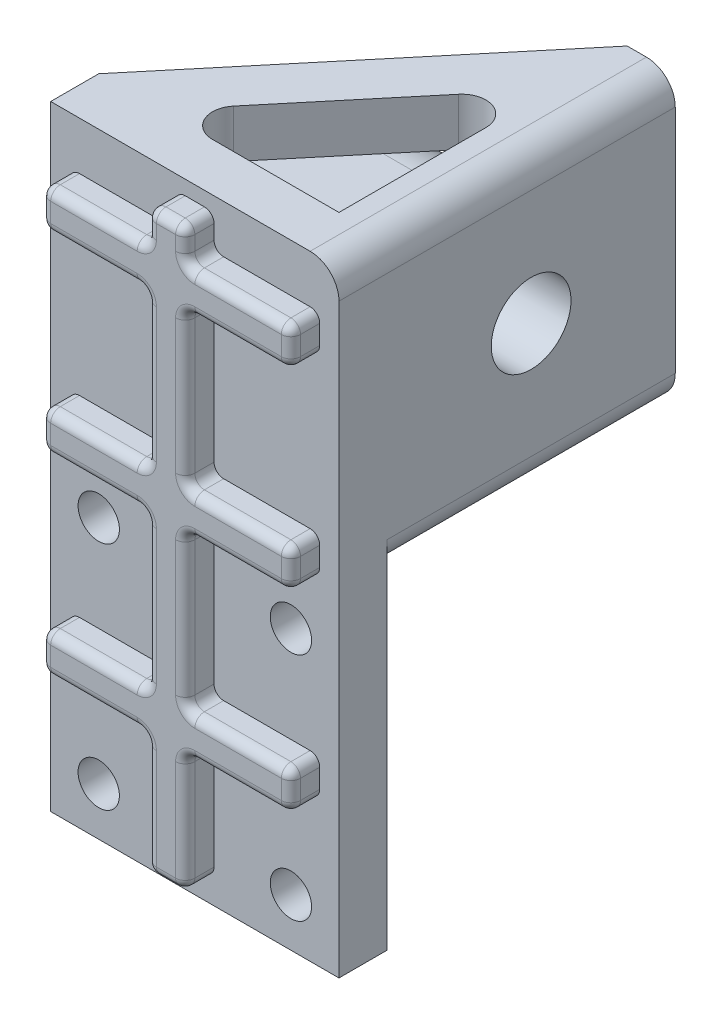
SolidWorks part; units mm, degrees
material "Balsa"
ref_plane "前视基准面" through (0, 0, 0) normal (0, 0, 1) x (1, 0, 0)
ref_plane "上视基准面" through (0, 0, 0) normal (0, 1, 0) x (1, 0, 0)
ref_plane "右视基准面" through (0, 0, 0) normal (1, 0, 0) x (0, 0, -1)
other "Configuration Table"
sketch "Sketch3" plane through (0, 0, 0) normal (0, 0, 1) x (1, 0, 0)
  line L0 (15, 0) -> (15, -34) construction
  line L1 (0, 0) -> (30, 0)
  line L2 (0, 0) -> (0, -34)
  line L3 (0, -34) -> (30, -34)
  line L4 (30, 0) -> (30, -34)
  line L5 (0, -17) -> (30, -17) construction
  circle A0 centre (5, -5) radius 2.15
  circle A1 centre (25, -5) radius 2.15
  circle A2 centre (5, -29) radius 2.15
  circle A3 centre (25, -29) radius 2.15
  point P6 (15, 0)
  dimension "D3" = 4.3
  dimension "D4" = 20
  dimension "D5" = 24
  dimension "D1" = 34
  dimension "D2" = 30
extrude "Boss-Extrude1" add sketch "Sketch3" along normal blind 5
sketch "Sketch5" plane through (0, 0, 0) normal (0, 0, -1) x (-1, 0, 0)
  line L1 (-30, 0) -> (0, 0)
  line L2 (-30, 0) -> (-30, 30)
  line L3 (-30, 30) -> (0, 30)
  line L4 (0, 0) -> (0, 30)
  line L5 (-30, 30) -> (-25, 30)
  line L6 (-30, 30) -> (-30, 0)
  line L7 (-30, 0) -> (-25, 0)
  line L8 (-25, 30) -> (-25, 0)
  dimension "D1" = 30
  dimension "D2" = 5
  dimension "D3" = 30
extrude "Boss-Extrude4" add sketch "Sketch5" against normal up to surface (5 mm away) contours L2 L1 L4 L3 | L6 L5 L8 L7 up to face at (2.85, -29, 5)
sketch "Sketch6" plane through (0, 0, 0) normal (0, 0, -1) x (-1, 0, 0)
  line L0 (-30, 0) -> (-30, 30) construction
  line L1 (-30, 0) -> (0, 0) construction
  line L2 (0, 0) -> (0, 30) construction
  line L3 (-30, 30) -> (0, 30) construction
  line L4 (-30, 30) -> (-25, 30) construction
  line L5 (-25, 30) -> (-25, 0) construction
  line L6 (-30, 0) -> (-25, 0) construction
  line L7 (-30, 30) -> (-30, 0) construction
  line L8 (-30, 0) -> (-30, 30)
  line L9 (-30, 0) -> (0, 0)
  line L10 (0, 0) -> (0, 30)
  line L11 (-30, 30) -> (0, 30)
  line L12 (-30, 30) -> (-25, 30)
  line L13 (-25, 30) -> (-25, 0)
  line L14 (-30, 0) -> (-25, 0)
  line L15 (-30, 30) -> (-30, 0)
  line M3 (-30, 30) -> (-30, -34)
extrude "Boss-Extrude5" add sketch "Sketch6" along normal blind 30 contours L13 L11 L9 M3
sketch "Sketch7" plane through (0, 0, 5) normal (0, 0, 1) x (1, 0, 0)
  line L0 (15, 30) -> (15, -34) construction
  line L1 (30, 30) -> (0, 30) construction
  line L2 (0, -34) -> (30, -34) construction
  line L3 (2, 5) -> (2, 1)
  line L4 (13, 28.5) -> (17, 28.5)
  line L5 (13, 28.5) -> (13, -31.5)
  line L6 (13, -31.5) -> (17, -31.5)
  line L7 (17, 28.5) -> (17, -31.5)
  line L8 (2, -15) -> (28, -15)
  line L9 (2, -15) -> (2, -19)
  line L10 (2, -19) -> (28, -19)
  line L11 (28, -15) -> (28, -19)
  line L12 (2, 5) -> (28, 5)
  line L13 (28, 5) -> (28, 1)
  line L14 (2, 1) -> (28, 1)
  line L15 (2, 25) -> (2, 21)
  line L16 (2, 25) -> (28, 25)
  line L17 (28, 25) -> (28, 21)
  line L18 (2, 21) -> (28, 21)
  dimension "D1" = 4
  dimension "D2" = 2
  dimension "D3" = 60
  dimension "D4" = 2.5
  dimension "D5" = 13
  dimension "D6" = 26
  dimension "D7" = 15
  dimension "D8" = 4
  dimension "D10" = 20
  dimension "D9" = 3
extrude "Boss-Extrude6" add sketch "Sketch7" along normal blind 3 contours L7 L18 L17 L16 | L0 L4 L5 L16 | L4 L0 L16 L7 | L16 L0 L18 L7 | L0 L16 L5 L18 | L15 L18 L5 L16 | L0 L18 L5 L12 | L18 L0 L12 L7 | L12 L0 L14 L7 | L0 L12 L5 L14 | L3 L14 L5 L12 | L7 L14 L13 L12 | L14 L0 L8 L7 | L0 L14 L5 L8 | L9 L10 L5 L8 | L0 L8 L5 L10 | L8 L0 L10 L7 | L11 L8 L7 L10 | L10 L0 L6 L7 | L0 L10 L5 L6
fillet "Fillet1" radius 1 56 edges at (22.5, 25, 8) (17, 26.75, 8) (15, 28.5, 8) (13, 26.75, 8) (2, 23, 8) (7.5, 21, 8) (13, 13, 8) (7.5, 5, 8) (2, 3, 8) (7.5, 1, 8) (13, -7, 8) (7.5, -15, 8) (2, -17, 8) (7.5, -19, 8) (13, -25.25, 8) (15, -31.5, 8) (17, -25.25, 8) (22.5, -19, 8) (28, -17, 8) (22.5, -15, 8) (17, -7, 8) (22.5, 1, 8) (28, 3, 8) (22.5, 5, 8) (17, 13, 8) (22.5, 21, 8) (28, 23, 8) (28, 25, 6.5) (28, 21, 6.5) (17, 21, 6.5) (17, 5, 6.5) (28, 5, 6.5) (28, 1, 6.5) (17, 1, 6.5) (17, -15, 6.5) (28, -15, 6.5) (28, -19, 6.5) (17, -19, 6.5) (17, -31.5, 6.5) (13, -31.5, 6.5) (13, -19, 6.5) (2, -19, 6.5) (2, -15, 6.5) (13, -15, 6.5) (13, 1, 6.5) (2, 1, 6.5) (2, 5, 6.5) (13, 5, 6.5) (13, 21, 6.5) (2, 21, 6.5) (2, 25, 6.5) (13, 25, 6.5) (13, 28.5, 6.5) (17, 28.5, 6.5) (17, 25, 6.5) (7.5, 25, 8)
sketch "Sketch9" plane through (0, 30, 0) normal (0, 1, 0) x (1, 0, 0)
  line L0 (25, 22.1898) -> (6.5085, 0)
  line L1 (25, 30) -> (25, 0) construction
  line L2 (25, 0) -> (0, 0) construction
  line L3 (6.5085, 0) -> (0, 0)
  line L4 (0, 0) -> (25, 30)
  line L5 (25, 30) -> (25, 22.1898)
  dimension "D1" = 5
extrude "Boss-Extrude7" add sketch "Sketch9" against normal blind 5
sketch "Sketch10" plane through (0, 0, 0) normal (0, -1, 0) x (1, 0, 0)
  line L4 (25, -30) -> (25, -22.1898)
  line L5 (25, -22.1898) -> (6.5085, 0)
  line L6 (6.5085, 0) -> (0, 0)
  line L7 (0, 0) -> (25, -30)
  line L8 (25, -30) -> (25, -22.1898)
  line L9 (25, -22.1898) -> (6.5085, 0)
  line L10 (6.5085, 0) -> (0, 0)
  line L11 (0, 0) -> (25, -30)
  dimension "D1" = 0
extrude "Boss-Extrude8" add sketch "Sketch10" against normal blind 5
fillet "Fillet2" radius 2.5 4 edges at (25, 2.5, -22.1898) (6.5085, 2.5, 0) (25, 27.5, -22.1898) (6.5085, 27.5, 0)
sketch "Sketch11" plane through (25, 0, 0) normal (-1, 0, 0) x (0, 0, 1)
  line L0 (0, 5) -> (-30, 5) construction
  line L1 (0, 25) -> (0, 5) construction
  line L2 (0, 5) -> (-30, 5)
  line L3 (0, 25) -> (0, 5)
  circle A0 centre (-15, 15) radius 4.15
  dimension "D2" = 8.3
  dimension "D1" = 15
  dimension "D3" = 10
extrude "Cut-Extrude1" cut sketch "Sketch11" against normal through all contours A0
fillet "Fillet3" radius 3 1 edges at (30, 30, -12.5)
fillet "Fillet4" radius 3 1 edges at (30, 0, -15)
sketch "Sketch13" plane through (25, 0, 0) normal (-1, 0, 0) x (0, 0, 1)
  line L0 (-15, 22.6) -> (0, 22.6)
  line L1 (0, 22.6) -> (0, 7.4)
  line L2 (0, 7.4) -> (-15, 7.4)
  line L8 (-30, 5) -> (-15.2846, 5)
  line L9 (-15.2846, 5) -> (-15.2846, 0)
  line L10 (-15.2846, 0) -> (0, 0)
  line L11 (0, 0) -> (0, 30)
  line L12 (0, 30) -> (-15.2846, 30)
  line L13 (-15.2846, 30) -> (-15.2846, 25)
  line L14 (-15.2846, 25) -> (-30, 25)
  line L15 (-30, 25) -> (-30, 5)
  line L16 (-30, 5) -> (-15.2846, 5)
  line L17 (-15.2846, 5) -> (-15.2846, 0)
  line L18 (-15.2846, 0) -> (0, 0)
  line L19 (0, 0) -> (0, 30)
  line L20 (0, 30) -> (-15.2846, 30)
  line L21 (-15.2846, 30) -> (-15.2846, 25)
  line L22 (-15.2846, 25) -> (-30, 25)
  line L23 (-30, 25) -> (-30, 5)
  arc A0 (-15, 22.6) -> (-15, 7.4) centre (-15, 15) ccw
  circle M9 centre (-15, 15) radius 4.15
  line M13 (0, 0) -> (0, 30)
  dimension "D2" = 15.2
  dimension "D1" = 0
extrude "Boss-Extrude9" add sketch "Sketch13" along normal blind 20 contours L0 A0 L2 M13 M9
fillet "Fillet5" radius 2 3 edges at (15, 22.6, 0) (5, 15, 0) (15, 7.4, 0)
